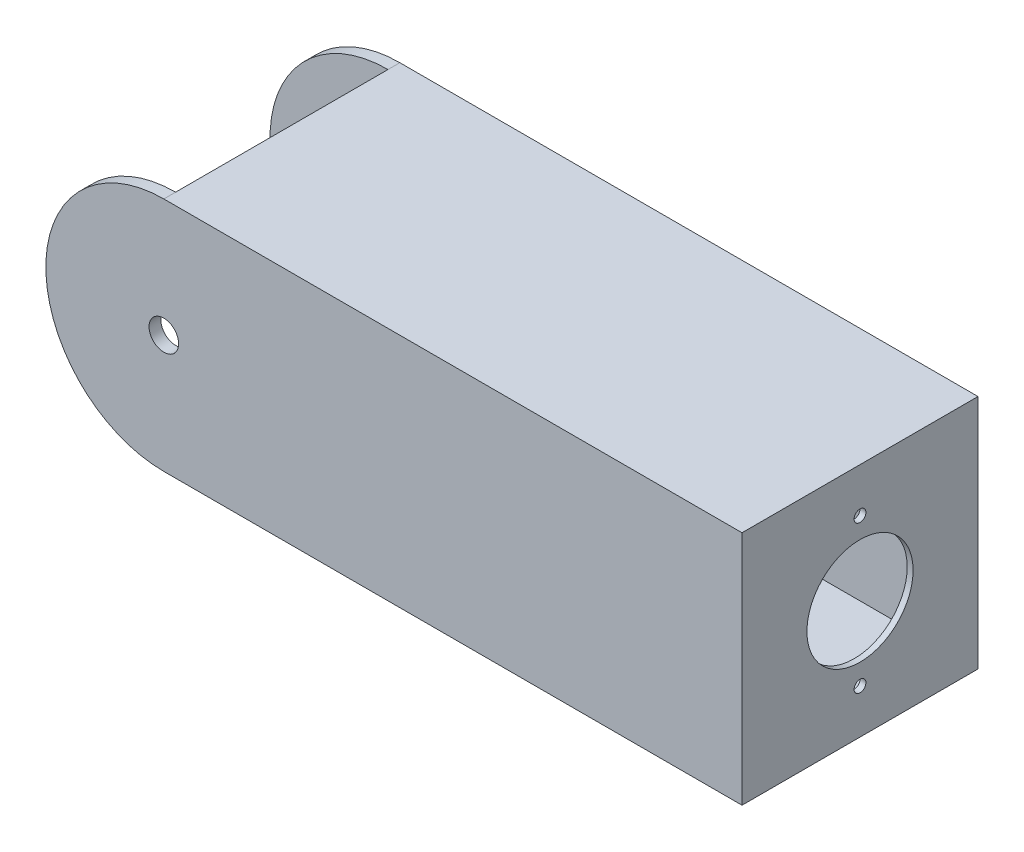
SolidWorks part; units mm, degrees
ref_plane "Front Plane" through (0, 0, 0) normal (0, 0, 1) x (1, 0, 0)
ref_plane "Top Plane" through (0, 0, 0) normal (0, 1, 0) x (1, 0, 0)
ref_plane "Right Plane" through (0, 0, 0) normal (1, 0, 0) x (0, 0, -1)
sketch "Sketch2" plane through (0, 0, 0) normal (0, 0, 1) x (1, 0, 0)
  line L1 (-50.8, 25.4) -> (73.66, 25.4)
  line L3 (-50.8, -25.4) -> (73.66, -25.4)
  line L4 (73.66, 25.4) -> (73.66, -25.4)
  arc A0 (-50.8, 25.4) -> (-50.8, -25.4) centre (-50.8, 0) ccw
  circle A1 centre (-50.8, 0) radius 3.1813
  point P1 (0, 0)
  dimension "D1" = 6.3627
  dimension "D2" = 50.8
  dimension "D3" = 25.4
  dimension "D4" = 124.46
  dimension "D6" = 73.66
extrude "Boss-Extrude1" add sketch "Sketch2" against normal mid plane 50.8
sketch "Sketch5" plane through (0, 0, 0) normal (1, 0, 0) x (0, 0, -1)
  line L1 (-22.86, -22.86) -> (22.86, -22.86)
  line L2 (-22.86, -22.86) -> (-22.86, 22.86)
  line L3 (-22.86, 22.86) -> (22.86, 22.86)
  line L4 (22.86, -22.86) -> (22.86, 22.86)
  line L5 (-22.86, -22.86) -> (22.86, 22.86) construction
  line L6 (-22.86, 22.86) -> (22.86, -22.86) construction
  point P0 (0, 0)
  dimension "D1" = 45.72
  dimension "D2" = 45.72
extrude "Cut-Extrude1" cut sketch "Sketch5" against normal mid plane 144.78
sketch "Sketch6" plane through (0, 0, 0) normal (0, 1, 0) x (1, 0, 0)
  line L0 (-50.8, 25.4) -> (-50.8, -25.4) construction
  line L1 (-96.52, -22.86) -> (-50.8, -22.86)
  line L2 (-96.52, -22.86) -> (-96.52, 22.86)
  line L3 (-96.52, 22.86) -> (-50.8, 22.86)
  line L4 (-50.8, -22.86) -> (-50.8, 22.86)
  line L5 (-96.52, -22.86) -> (-50.8, 22.86) construction
  line L6 (-96.52, 22.86) -> (-50.8, -22.86) construction
  point P0 (-73.66, 0)
  dimension "D1" = 45.72
  dimension "D2" = 45.72
extrude "Cut-Extrude2" cut sketch "Sketch6" against normal mid plane 167.64
sketch "Sketch8" plane through (73.66, 0, 0) normal (1, 0, 0) x (0, 0, -1)
  circle A0 centre (0, 0) radius 11.43
  circle A1 centre (0, 15.875) radius 1.27
  circle A2 centre (0, -15.875) radius 1.27
  dimension "D1" = 22.86
  dimension "D4" = 2.54
  dimension "D5" = 2.54
  dimension "D2" = 15.875
  dimension "D3" = 15.875
extrude "Cut-Extrude3" cut sketch "Sketch8" against normal up to next
